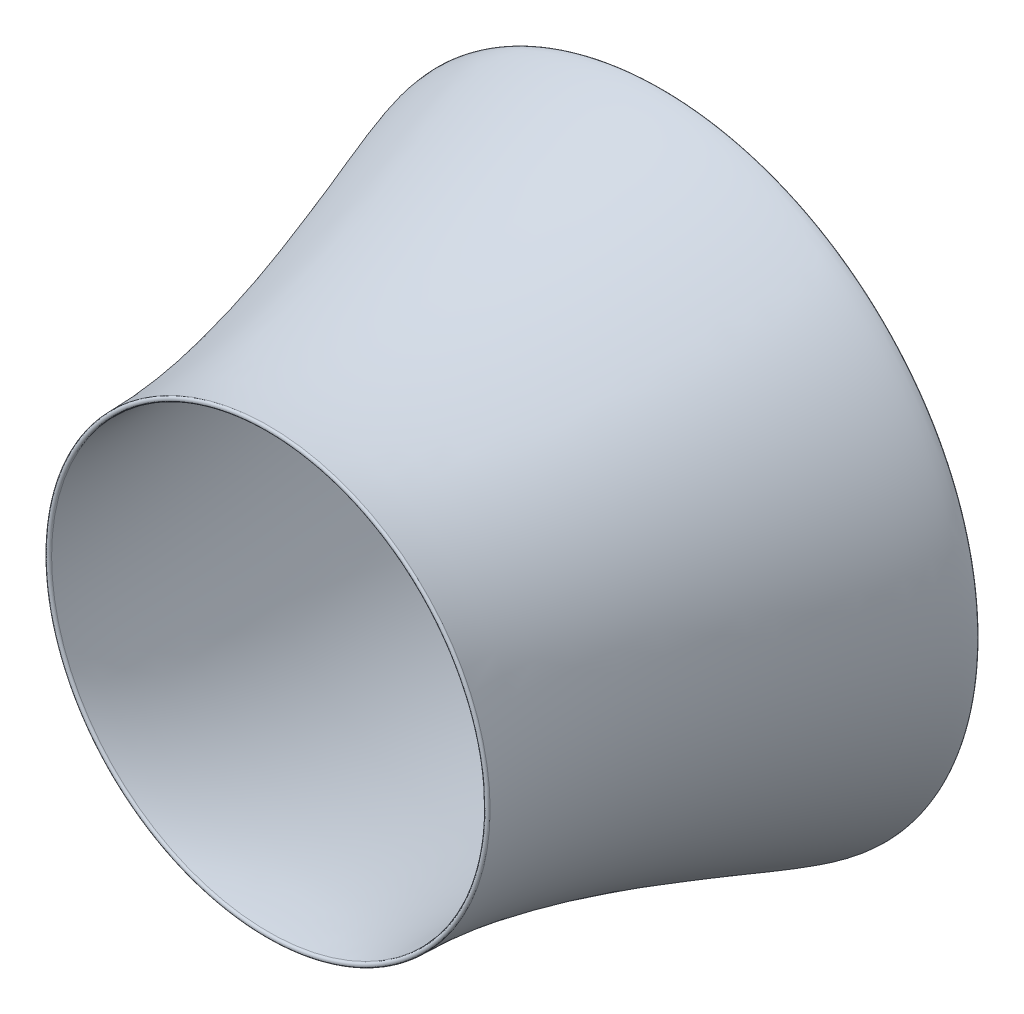
SolidWorks part; units mm, degrees
ref_plane "Front Plane" through (0, 0, 0) normal (0, 0, 1) x (1, 0, 0)
ref_plane "Top Plane" through (0, 0, 0) normal (0, 1, 0) x (1, 0, 0)
ref_plane "Right Plane" through (0, 0, 0) normal (1, 0, 0) x (0, 0, -1)
sketch "Sketch1" plane through (0, 0, 0) normal (0, 0, 1) x (1, 0, 0)
  circle A0 centre (0, 0) radius 50.8
  dimension "D1" = 101.6
ref_plane "Plane1" through (0, -254, 0) normal (0, 1, 0) x (1, 0, 0)
sketch "Sketch6" plane through (0, 0, 0) normal (0, 1, 0) x (1, 0, 0)
  line L0 (0, -99.6848) -> (0, 145.6048) construction
ref_plane "Plane2" through (0, -114.3, 0) normal (0, 1, 0) x (1, 0, 0)
sketch "Sketch12" plane through (0, 0, 0) normal (0, 1, 0) x (1, 0, 0)
  line L0 (0, -1104.7568) -> (0, -908.6135) construction
ref_plane "Plane3" through (0, 0, 203.2) normal (0, 0, 1) x (1, 0, 0)
ref_plane "Plane4" through (0, 0, 889) normal (0, 0, 1) x (1, 0, 0)
sketch "Sketch17" plane through (0, 0, 0) normal (0, 1, 0) x (1, 0, 0)
  line L0 (-259.4955, -43.5301) -> (-259.4955, 70.1436) construction
  line L1 (-110.6437, -1316.1124) -> (-110.6437, -853.5386) construction
  line L2 (-259.4955, 45.4622) -> (-387.328, 45.4622)
  line L3 (-387.328, 45.4622) -> (-387.328, -1084.8928)
  line L4 (-387.328, -1084.8928) -> (-110.6437, -1084.8928)
  spline S0 degree 3 poles (-259.4955, 45.4622) (-259.4955, -7.1736) (-207.7477, -105.8122) (-173.3147, -383.1384) (-92.4228, -818.9689) (-110.6437, -795.7842) (-110.6437, -1084.8928) knots 0 0 0 0 0.158009 0.206507 0.484977 1 1 1 1
sketch "Sketch21" plane through (0, 0, 0) normal (0, 1, 0) x (1, 0, 0)
  line L0 (-1447.7159, -22.8536) -> (-1447.7159, 113.778) construction
  line L1 (-1013.8833, -1315.9117) -> (-1013.8833, -853.874) construction
  line L2 (-1232.8269, 94.6857) -> (-1447.7159, 94.6857) construction
  line L3 (-992.1802, -1702.1648) -> (-1013.8833, -1702.1648) construction
  line L4 (-992.1802, -1702.1648) -> (-1013.8833, -1702.1648)
  line L6 (-1232.8269, 94.6857) -> (-1447.7159, 94.6857)
  spline S0 degree 3 poles (-1232.8269, 94.6857) (-1182.7122, -46.3816) (-1110.5026, -571.313) (-953.7634, -1319.3047) (-992.1802, -1702.1648) knots 0 0 0 0 0.206507 1 1 1 1
  spline S1 degree 3 poles (-1447.7159, 94.6857) (-1447.7159, -30.6982) (-1013.8833, -971.8557) (-1013.8833, -1702.1648) knots 0 0 0 0 1 1 1 1
  point P10 (-407.6556, -1400.4871)
  point P11 (-476.3229, -456.3121)
  point P12 (0, 0)
  point P13 (-1013.8833, -1385.2106)
  point P14 (-949.0111, -1608.2087)
  point P15 (-653.0319, -254.0022)
  point P16 (-1447.7159, 50.0861)
  point P17 (-1232.8269, 94.6857)
  point P18 (-1115.2461, -432.4006)
  point P19 (-1013.8833, -712.1618)
  point P20 (0, 0)
  point P21 (-992.1802, -1702.1648)
  point P22 (-1064.048, -786.4298)
  point P23 (-1157.4947, -220.195)
revolve "Revolve2" add sketch "Sketch21" angle 360 about L0
sketch "Sketch22" plane through (0, 0, 0) normal (0, 1, 0) x (1, 0, 0)
  line L0 (-1447.7159, 94.6857) -> (-1232.8269, 94.6857)
  line L1 (-1232.8269, 90.8767) -> (-1232.8269, 98.4948) construction
  line L2 (-1447.7159, 96.0785) -> (-1447.7159, 93.293) construction
  spline S0 degree 3 poles (-1447.7159, 94.6857) (-1447.7159, 111.6191) (-1232.8269, 111.6191) (-1232.8269, 94.6857) knots 0 0 0 0 1 1 1 1
revolve "Revolve3" add sketch "Sketch22" angle 360 about L0
sketch "Sketch23" plane through (0, 0, 0) normal (0, 1, 0) x (1, 0, 0)
  line L0 (-1013.8833, -1702.1648) -> (-992.1802, -1702.1648)
  line L1 (-1013.8833, -1711.3759) -> (-1013.8833, -1692.9538) construction
  line L2 (-992.1802, -1691.5918) -> (-992.1802, -1712.7378) construction
  spline S0 degree 3 poles (-1013.8833, -1702.1648) (-1013.8833, -1714.8648) (-992.1802, -1714.8648) (-992.1802, -1702.1648) knots 0 0 0 0 1 1 1 1
revolve "Revolve4" add sketch "Sketch23" angle 360 about L0
ref_plane "Plane5" through (289.9098, 0, 0) normal (1, 0, 0) x (0, 0, -1)
sketch "Sketch24" plane through (289.9098, 0, 0) normal (1, 0, 0) x (0, 0, -1)
  line L0 (-1123.5724, -17.6357) -> (119.2276, -17.6357) construction
  line L1 (-1702.1648, 0) -> (94.6857, 0) construction
  line L2 (-1702.1648, -1013.8833) -> (-1702.1648, 1013.8833) construction
  line L3 (94.6857, 1447.7159) -> (94.6857, -1447.7159) construction
  text T0 "MD-130 Gas Turbine Engine" font "TI-Nspire" height in points 160
